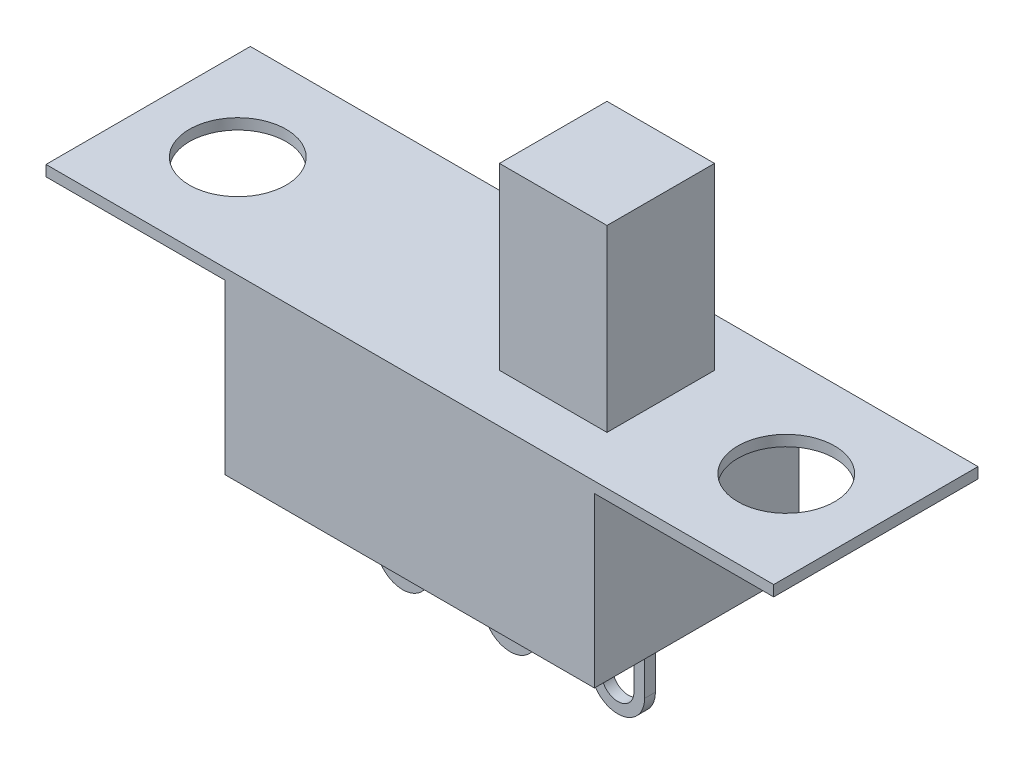
SolidWorks part; units mm, degrees
material "1060 Alloy"
ref_plane "Front Plane" through (0, 0, 0) normal (0, 0, 1) x (1, 0, 0)
ref_plane "Top Plane" through (0, 0, 0) normal (0, 1, 0) x (1, 0, 0)
ref_plane "Right Plane" through (0, 0, 0) normal (1, 0, 0) x (0, 0, -1)
sketch "Sketch1" plane through (0, 0, 0) normal (0, 0, 1) x (1, 0, 0)
  line L1 (-5.15, -2.5) -> (5.15, -2.5)
  line L2 (-5.15, -2.5) -> (-5.15, 2.5)
  line L3 (-5.15, 2.5) -> (5.15, 2.5)
  line L4 (5.15, -2.5) -> (5.15, 2.5)
  line L5 (-5.15, -2.5) -> (5.15, 2.5) construction
  line L6 (-5.15, 2.5) -> (5.15, -2.5) construction
  point P0 (0, 0)
  dimension "D1" = 10.3
  dimension "D2" = 5
extrude "Boss-Extrude1" add sketch "Sketch1" along normal mid plane 5.7
sketch "Sketch2" plane through (5.15, 0, 0) normal (1, 0, 0) x (0, 0, -1)
  line L0 (2.85, -2.5) -> (2.85, 2.5) construction
  line L1 (-2.85, 2.5) -> (2.85, 2.5)
  line L2 (-2.85, 2.5) -> (-2.85, 2.2)
  line L3 (-2.85, 2.2) -> (2.85, 2.2)
  line L4 (2.85, 2.5) -> (2.85, 2.2)
  dimension "D1" = 0.3
extrude "Boss-Extrude2" add sketch "Sketch2" along normal blind 5
sketch "Sketch3" plane through (0, 2.5, 0) normal (0, 1, 0) x (1, 0, 0)
  line L0 (10.15, 2.85) -> (5.15, -2.85) construction
  circle A0 centre (7.65, 0) radius 1.35
  dimension "D1" = 2.7
extrude "Cut-Extrude1" cut sketch "Sketch3" against normal blind 5
mirror "Mirror1" about plane through (0, 0, 0) normal (1, 0, 0) of "Boss-Extrude2", "Cut-Extrude1"
sketch "Sketch4" plane through (0, 2.5, 0) normal (0, 1, 0) x (1, 0, 0)
  line L0 (5.15, -2.85) -> (5.15, 2.85) construction
  line L1 (4.15, -1.5) -> (1.15, -1.5)
  line L2 (4.15, -1.5) -> (4.15, 1.5)
  line L3 (4.15, 1.5) -> (1.15, 1.5)
  line L4 (1.15, -1.5) -> (1.15, 1.5)
  line L5 (4.15, -1.5) -> (1.15, 1.5) construction
  line L6 (4.15, 1.5) -> (1.15, -1.5) construction
  point P0 (2.65, 0)
  point P5 (0, 0)
  dimension "D1" = 3
  dimension "D2" = 1
extrude "Boss-Extrude3" add sketch "Sketch4" along normal blind 5
sketch "Sketch5" plane through (0, 0, 0) normal (0, 0, 1) x (1, 0, 0)
  line L0 (-3.65, -2.5) -> (-2.15, -2.5)
  line L1 (-5.15, -2.5) -> (5.15, -2.5) construction
  line L2 (-2.15, -2.5) -> (-2.15, -4.75)
  line L3 (-3.65, -4.75) -> (-3.65, -2.5)
  line L4 (-5.15, 2.2) -> (-5.15, -2.5) construction
  line L5 (-2.9, -4.15) -> (-2.9, -4.75) construction
  line L6 (-2.45, -4.15) -> (-2.45, -4.75)
  line L7 (-3.35, -4.15) -> (-3.35, -4.75)
  arc A0 (-2.15, -4.75) -> (-3.65, -4.75) centre (-2.9, -4.75) cw
  arc A1 (-2.45, -4.15) -> (-3.35, -4.15) centre (-2.9, -4.15) ccw
  arc A2 (-3.35, -4.75) -> (-2.45, -4.75) centre (-2.9, -4.75) ccw
  point P9 (-2.9, -5.5)
  point P12 (-2.9, -4.45)
  point P17 (-2.9, -3.7)
  point P18 (-2.9, -5.2)
  dimension "D1" = 1.5
  dimension "D2" = 1.5
  dimension "D3" = 3
  dimension "D4" = 1.5
  dimension "D5" = 0.3
extrude "Boss-Extrude4" add sketch "Sketch5" along normal mid plane 0.3
pattern_linear "LPattern1" count 3 spacing 3 along (1, 0, 0) of "Boss-Extrude4"
